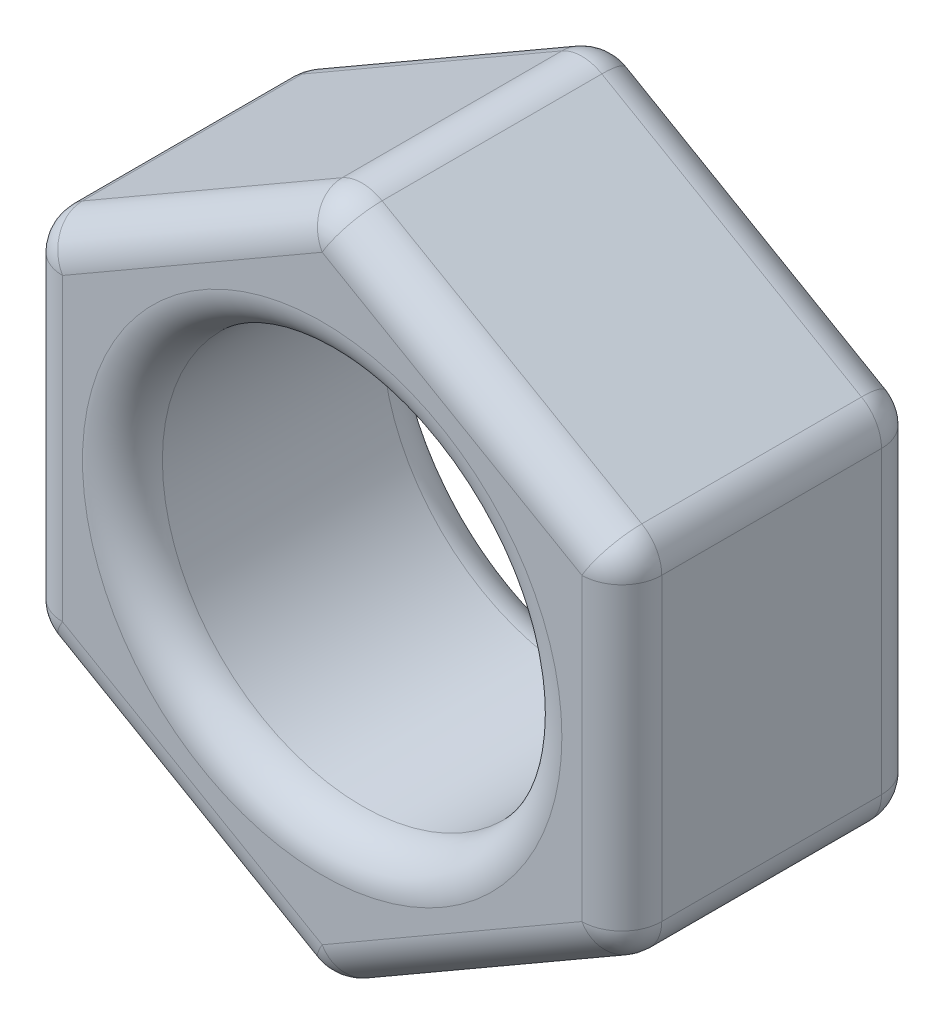
SolidWorks part; units mm, degrees
material "Chrome Stainless Steel"
ref_plane "Front Plane" through (0, 0, 0) normal (0, 0, 1) x (1, 0, 0)
ref_plane "Top Plane" through (0, 0, 0) normal (0, 1, 0) x (1, 0, 0)
ref_plane "Right Plane" through (0, 0, 0) normal (1, 0, 0) x (0, 0, -1)
sketch "Sketch1" plane through (0, 0, 0) normal (0, 0, 1) x (1, 0, 0)
  line L1 (0, -1.7321) -> (1.5, -0.866)
  line L2 (1.5, -0.866) -> (1.5, 0.866)
  line L3 (1.5, 0.866) -> (0, 1.7321)
  line L4 (0, 1.7321) -> (-1.5, 0.866)
  line L5 (-1.5, 0.866) -> (-1.5, -0.866)
  line L6 (-1.5, -0.866) -> (0, -1.7321)
  circle A0 centre (0, 0) radius 1.5 construction
  circle A1 centre (0, 0) radius 1
  dimension "D1" = 2
extrude "Extrude1" add sketch "Sketch1" along normal blind 1.5
fillet "Fillet1" radius 0.2 20 edges at (-0.75, 1.299, 1.5) (-0.75, 1.299, 0) (0.75, 1.299, 1.5) (0, 1.7321, 0.75) (0.75, 1.299, 0) (1.5, 0, 1.5) (1.5, 0.866, 0.75) (1.5, 0, 0) (0.75, -1.299, 1.5) (1.5, -0.866, 0.75) (0.75, -1.299, 0) (-0.75, -1.299, 1.5) (0, -1.7321, 0.75) (-0.75, -1.299, 0) (-1.5, 0.866, 0.75) (-1.5, 0, 1.5) (-1.5, -0.866, 0.75) (-1.5, 0, 0) (1, 0, 0) (1, 0, 1.5)
